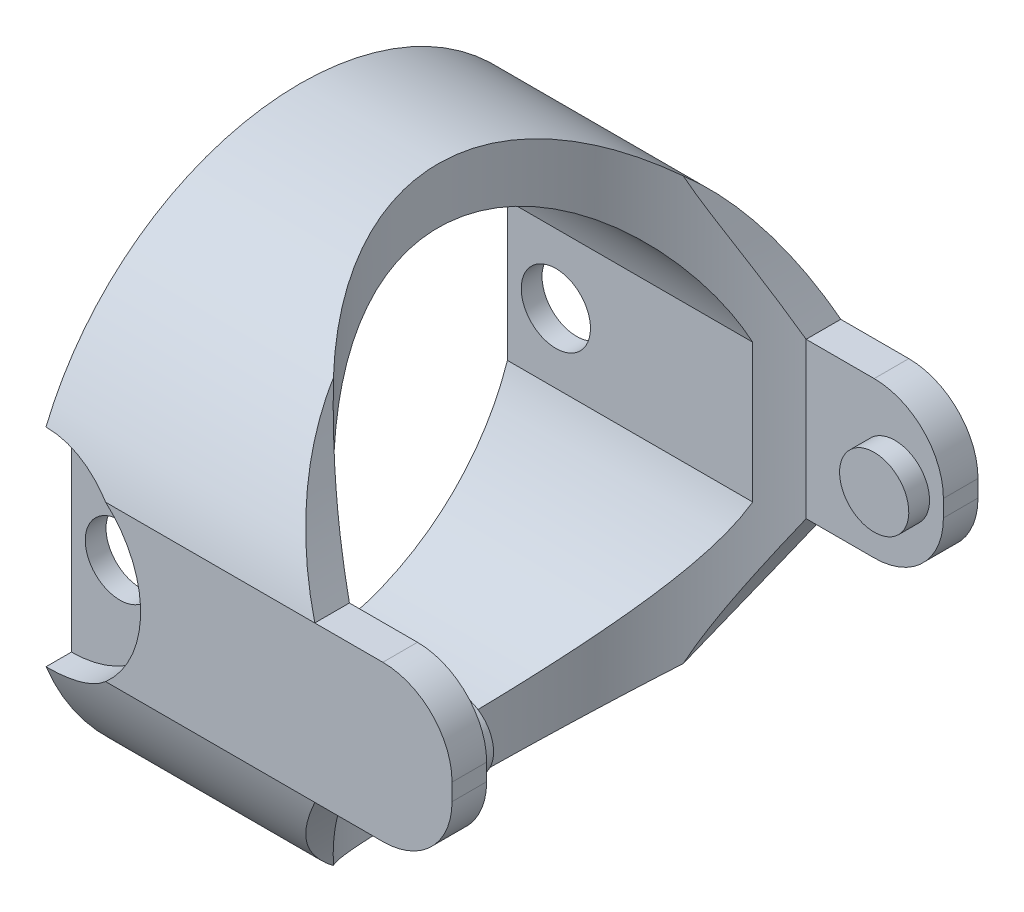
SolidWorks part; units mm, degrees
ref_plane "Płaszczyzna przednia" through (0, 0, 0) normal (0, 0, 1) x (1, 0, 0)
ref_plane "Płaszczyzna górna" through (0, 0, 0) normal (0, 1, 0) x (1, 0, 0)
ref_plane "Płaszczyzna prawa" through (0, 0, 0) normal (1, 0, 0) x (0, 0, -1)
sketch "Szkic4" plane through (0, 0, 0) normal (1, 0, 0) x (0, 0, -1)
  line L0 (-3, 1) -> (-3, -1)
  line L1 (3, 1) -> (3, -1)
  line L2 (0, -2.145) -> (0, 3.882) construction
  line L3 (3.8, 1.1223) -> (3.8, -1.1223)
  line L4 (-3.8, 1.1223) -> (-3.8, -1.1223)
  line L5 (3.8, 1.1223) -> (3.8, -1) construction
  arc A0 (-3, -1) -> (3, -1) centre (0, 0) ccw
  arc A1 (3, 1) -> (-3, 1) centre (0, 0) ccw
  arc A2 (3.8, 1.1223) -> (-3.8, 1.1223) centre (0, 0) ccw
  arc A3 (-3.8, -1.1223) -> (3.8, -1.1223) centre (0, 0) ccw
  arc A4 (-3.8, -1.1223) -> (3.7589, -1.253) centre (0, 0) ccw construction
  dimension "D1" = 2
  dimension "D2" = 2
  dimension "D3" = 6
  dimension "D4" = 0.8
extrude "Dodanie-wyciągnięcie2" add sketch "Szkic4" along normal blind 6 contours L4 A3 L3 A2 A1 L1 A0 L0
sketch "Szkic6" plane through (0, 0, 0) normal (0, 1, 0) x (1, 0, 0)
  ellipse E0 centre (6, 0) end of major axis (2, 0) minor radius 3.8
  dimension "D1" = 4
extrude "Wytnij-wyciągnięcie4" cut sketch "Szkic6" against normal through all and the other way through all
sketch "Szkic10" plane through (0, 0, 3.8) normal (0, 0, 1) x (1, 0, 0)
  line L4 (0, 1.1223) -> (0, -1.1223)
  line L5 (0, -1.1223) -> (6, -1.1223)
  line L6 (6, -1.1223) -> (6, 1.1223)
  line L7 (6, 1.1223) -> (0, 1.1223)
  line L8 (0, 1.1223) -> (0, -1.1223)
  line L9 (0, -1.1223) -> (6, -1.1223)
  line L10 (6, -1.1223) -> (6, 1.1223)
  line L11 (6, 1.1223) -> (0, 1.1223)
  dimension "D1" = 0
extrude "Dodanie-wyciągnięcie5" add sketch "Szkic10" against normal blind 0.5
sketch "Szkic11" plane through (0, 0, 3.3) normal (0, 0, -1) x (-1, 0, 0)
  line L0 (-2.8717, -3.6223) -> (-6, -3.6223)
  line L1 (-4.0167, 0) -> (-6, 0) construction
  line L2 (-2.8717, 3.6223) -> (-6, 3.6223)
  line L3 (-6, -3.6223) -> (-6, -1.1223)
  line L4 (-6, -1.1223) -> (-4.0167, -1.1223)
  line L5 (-4.0167, -1.1223) -> (-4.0167, 1.1223)
  line L6 (-4.0167, 1.1223) -> (-6, 1.1223)
  line L7 (-6, 1.1223) -> (-6, -1.1223)
  line L8 (-6, -1.1223) -> (-4.0167, -1.1223)
  line L9 (-4.0167, -1.1223) -> (-4.0167, 1.1223)
  line L10 (-4.0167, 1.1223) -> (-6, 1.1223)
  line L11 (-6, 1.1223) -> (-6, -1.1223)
  line L12 (-6, 3.6223) -> (-6, 1.1223)
  spline S0 degree 2 poles (-4.0167, -1.1223) (-2.9256, -2.9039) (-2.8717, -3.6223) knots 0 0 0 1 1 1
  spline S1 degree 2 poles (-4.0167, 1.1223) (-2.9256, 2.9039) (-2.8717, 3.6223) knots 0 0 0 1 1 1
  dimension "D2" = 2.5
  dimension "D1" = 0
extrude "Wytnij-wyciągnięcie6" cut sketch "Szkic11" against normal through all and the other way through all
mirror "Lustro2" about plane through (0, 0, 0) normal (0, 0, 1) of "Dodanie-wyciągnięcie5"
fillet "Zaokrąglenie3" radius 1 4 edges at (6, -1.1223, 3.55) (6, 1.1223, 3.55) (6, 1.1223, -3.55) (6, -1.1223, -3.55)
sketch "Szkic12" plane through (0, 0, -3.8) normal (0, 0, -1) x (-1, 0, 0)
  line L0 (-6, 0.1223) -> (-6, -0.1223) construction
  circle A0 centre (-5.3, 0) radius 0.5
  point P2 (-6, 0)
  dimension "D1" = 1
  dimension "D2" = 0.7
sketch "Szkic13" plane through (0, 0, 3.8) normal (0, 0, 1) x (1, 0, 0)
  line L0 (0, 3.9623) -> (0, 1.1223) construction
  line L2 (0, 1.5) -> (0, -1.5)
  arc A0 (0, -1.5) -> (0, 1.5) centre (0, 0) ccw
  dimension "D1" = 1.5
extrude "Wytnij-wyciągnięcie8" cut sketch "Szkic13" against normal blind 0.5
mirror "Lustro3" about plane through (0, 0, 0) normal (0, 0, 1) of "Wytnij-wyciągnięcie8"
sketch "Szkic14" plane through (0, 0, 3.3) normal (0, 0, 1) x (1, 0, 0)
  line L0 (0, 1.5) -> (0, -1.5) construction
  circle A0 centre (0.7, 0) radius 0.5
  dimension "D1" = 1
  dimension "D2" = 0.7
extrude "Wytnij-wyciągnięcie9" cut sketch "Szkic14" against normal through all
extrude "Dodanie-wyciągnięcie6" add sketch "Szkic12" against normal blind 0.8
mirror "Lustro4" about plane through (0, 0, 0) normal (0, 0, 1) of "Dodanie-wyciągnięcie6"
scale "Skala1" scale about centroid uniform scaling yes scale factor 0.35
